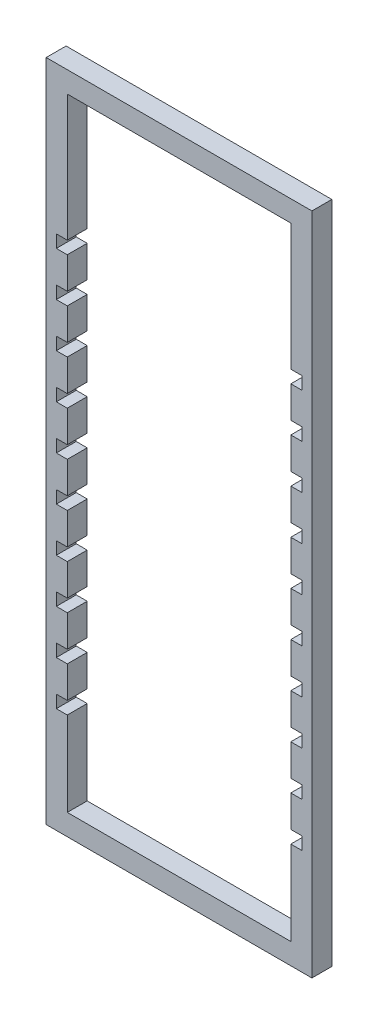
SolidWorks part; units mm, degrees
ref_plane "Front Plane" through (0, 0, 0) normal (0, 0, 1) x (1, 0, 0)
ref_plane "Top Plane" through (0, 0, 0) normal (0, 1, 0) x (1, 0, 0)
ref_plane "Right Plane" through (0, 0, 0) normal (1, 0, 0) x (0, 0, -1)
sketch "Sketch1" plane through (0, 0, 0) normal (0, 0, 1) x (1, 0, 0)
  line L0 (40.005, 193.675) -> (40.005, 0) construction
  line L1 (0, 0) -> (6.35, 0)
  line L2 (0, 0) -> (0, 200.025)
  line L3 (0, 200.025) -> (6.35, 200.025)
  line L4 (6.35, 6.35) -> (6.35, 193.675)
  line L5 (6.35, 200.025) -> (73.66, 200.025)
  line L7 (6.35, 193.675) -> (73.66, 193.675)
  line L9 (80.01, 200.025) -> (73.66, 200.025)
  line L10 (73.66, 6.35) -> (73.66, 193.675)
  line L11 (80.01, 0) -> (73.66, 0)
  line L12 (80.01, 0) -> (80.01, 200.025)
  line L13 (6.35, 100.0125) -> (73.66, 100.0125) construction
  line L14 (6.35, 6.35) -> (73.66, 6.35)
  line L16 (6.35, 0) -> (73.66, 0)
  dimension "D1" = 200.025
  dimension "D2" = 6.35
  dimension "D3" = 6.35
  dimension "D4" = 67.31
  dimension "D5" = 67.31
  dimension "D6" = 6.35
extrude "Boss-Extrude1" add sketch "Sketch1" against normal blind 5.9944
sketch "Sketch2" plane through (0, 0, 0) normal (0, 0, 1) x (1, 0, 0)
  line L0 (6.35, 193.675) -> (6.35, 6.35) construction
  line L1 (3.048, 31.75) -> (9.652, 31.75)
  line L2 (3.048, 31.75) -> (3.048, 35.56)
  line L3 (3.048, 35.56) -> (9.652, 35.56)
  line L4 (9.652, 31.75) -> (9.652, 35.56)
  line L5 (3.048, 31.75) -> (9.652, 35.56) construction
  line L6 (3.048, 35.56) -> (9.652, 31.75) construction
  line L7 (0, 0) -> (80.01, 0) construction
  line L8 (3.048, 45.085) -> (3.048, 48.895)
  line L11 (76.962, 35.56) -> (70.358, 35.56)
  line L12 (70.358, 31.75) -> (70.358, 35.56)
  line L13 (76.962, 31.75) -> (70.358, 31.75)
  line L14 (76.962, 31.75) -> (76.962, 35.56)
  line L71 (3.048, 45.085) -> (9.652, 45.085)
  line L72 (9.652, 45.085) -> (9.652, 48.895)
  line L73 (3.048, 48.895) -> (9.652, 48.895)
  line L74 (76.962, 48.895) -> (70.358, 48.895)
  line L75 (70.358, 45.085) -> (70.358, 48.895)
  line L76 (76.962, 45.085) -> (70.358, 45.085)
  line L77 (76.962, 45.085) -> (76.962, 48.895)
  line L78 (3.048, 58.42) -> (3.048, 62.23)
  line L79 (3.048, 58.42) -> (9.652, 58.42)
  line L80 (9.652, 58.42) -> (9.652, 62.23)
  line L81 (3.048, 62.23) -> (9.652, 62.23)
  line L82 (76.962, 62.23) -> (70.358, 62.23)
  line L83 (70.358, 58.42) -> (70.358, 62.23)
  line L84 (76.962, 58.42) -> (70.358, 58.42)
  line L85 (76.962, 58.42) -> (76.962, 62.23)
  line L86 (3.048, 71.755) -> (3.048, 75.565)
  line L87 (3.048, 71.755) -> (9.652, 71.755)
  line L88 (9.652, 71.755) -> (9.652, 75.565)
  line L89 (3.048, 75.565) -> (9.652, 75.565)
  line L90 (76.962, 75.565) -> (70.358, 75.565)
  line L91 (70.358, 71.755) -> (70.358, 75.565)
  line L92 (76.962, 71.755) -> (70.358, 71.755)
  line L93 (76.962, 71.755) -> (76.962, 75.565)
  line L94 (3.048, 85.09) -> (3.048, 88.9)
  line L95 (3.048, 85.09) -> (9.652, 85.09)
  line L96 (9.652, 85.09) -> (9.652, 88.9)
  line L97 (3.048, 88.9) -> (9.652, 88.9)
  line L98 (76.962, 88.9) -> (70.358, 88.9)
  line L99 (70.358, 85.09) -> (70.358, 88.9)
  line L100 (76.962, 85.09) -> (70.358, 85.09)
  line L101 (76.962, 85.09) -> (76.962, 88.9)
  line L102 (3.048, 98.425) -> (3.048, 102.235)
  line L103 (3.048, 98.425) -> (9.652, 98.425)
  line L104 (9.652, 98.425) -> (9.652, 102.235)
  line L105 (3.048, 102.235) -> (9.652, 102.235)
  line L106 (76.962, 102.235) -> (70.358, 102.235)
  line L107 (70.358, 98.425) -> (70.358, 102.235)
  line L108 (76.962, 98.425) -> (70.358, 98.425)
  line L109 (76.962, 98.425) -> (76.962, 102.235)
  line L110 (3.048, 111.76) -> (3.048, 115.57)
  line L111 (3.048, 111.76) -> (9.652, 111.76)
  line L112 (9.652, 111.76) -> (9.652, 115.57)
  line L113 (3.048, 115.57) -> (9.652, 115.57)
  line L114 (76.962, 115.57) -> (70.358, 115.57)
  line L115 (70.358, 111.76) -> (70.358, 115.57)
  line L116 (76.962, 111.76) -> (70.358, 111.76)
  line L117 (76.962, 111.76) -> (76.962, 115.57)
  line L118 (3.048, 125.095) -> (3.048, 128.905)
  line L119 (3.048, 125.095) -> (9.652, 125.095)
  line L120 (9.652, 125.095) -> (9.652, 128.905)
  line L121 (3.048, 128.905) -> (9.652, 128.905)
  line L122 (76.962, 128.905) -> (70.358, 128.905)
  line L123 (70.358, 125.095) -> (70.358, 128.905)
  line L124 (76.962, 125.095) -> (70.358, 125.095)
  line L125 (76.962, 125.095) -> (76.962, 128.905)
  line L126 (3.048, 138.43) -> (3.048, 142.24)
  line L127 (3.048, 138.43) -> (9.652, 138.43)
  line L128 (9.652, 138.43) -> (9.652, 142.24)
  line L129 (3.048, 142.24) -> (9.652, 142.24)
  line L130 (76.962, 142.24) -> (70.358, 142.24)
  line L131 (70.358, 138.43) -> (70.358, 142.24)
  line L132 (76.962, 138.43) -> (70.358, 138.43)
  line L133 (76.962, 138.43) -> (76.962, 142.24)
  line L134 (3.048, 151.765) -> (3.048, 155.575)
  line L135 (3.048, 151.765) -> (9.652, 151.765)
  line L136 (9.652, 151.765) -> (9.652, 155.575)
  line L137 (3.048, 155.575) -> (9.652, 155.575)
  line L138 (76.962, 155.575) -> (70.358, 155.575)
  line L139 (70.358, 151.765) -> (70.358, 155.575)
  line L140 (76.962, 151.765) -> (70.358, 151.765)
  line L141 (76.962, 151.765) -> (76.962, 155.575)
  point P0 (6.35, 33.655)
  dimension "D1" = 6.604
  dimension "D2" = 10
  dimension "D3" = 31.75
extrude "Cut-Extrude1" cut sketch "Sketch2" against normal through all
